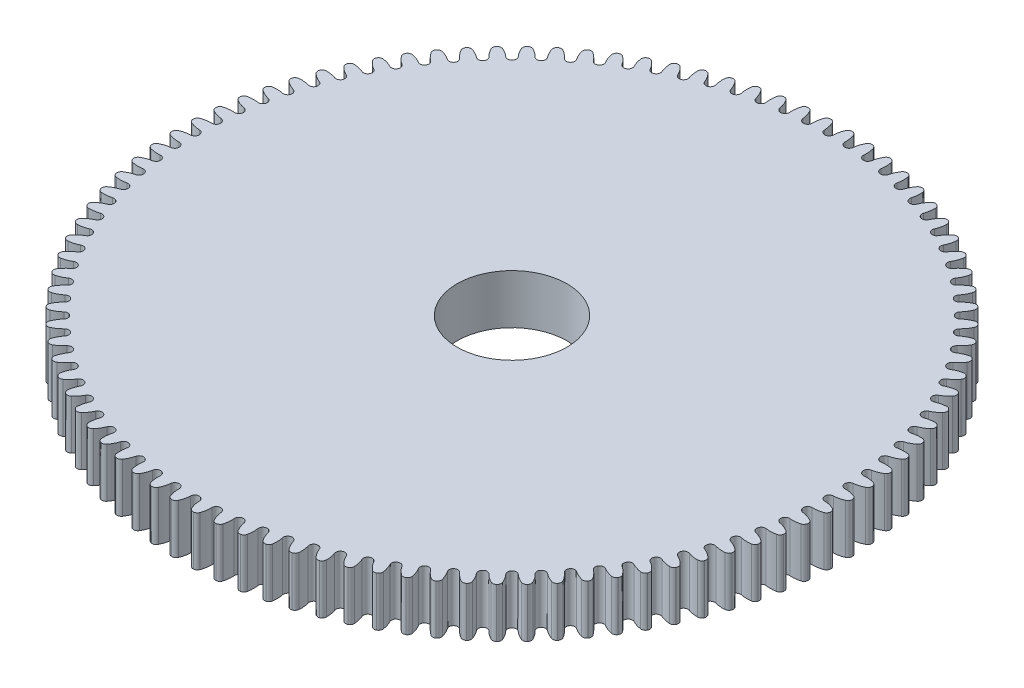
SolidWorks part; units mm, degrees
ref_plane "Front Plane" through (0, 0, 0) normal (0, 0, 1) x (1, 0, 0)
ref_plane "Top Plane" through (0, 0, 0) normal (0, 1, 0) x (1, 0, 0)
ref_plane "Right Plane" through (0, 0, 0) normal (1, 0, 0) x (0, 0, -1)
sketch "Sketch1" plane through (0, 0, 0) normal (0, 1, 0) x (1, 0, 0)
  circle A0 centre (0, 0) radius 60
  dimension "D1" = 120
extrude "Boss-Extrude1" add sketch "Sketch1" along normal blind 9
sketch "Sketch3" plane through (0, 0, 0) normal (0, -1, 0) x (1, 0, 0)
  line L0 (0, -57.718) -> (0, -60.2569) construction
  arc A0 (0.7992, -57.6813) -> (-0.7992, -57.6813) centre (0, -57.718) ccw
  arc A1 (0.7992, -57.6813) -> (1.2101, -59.4817) centre (5.9937, -57.4428) ccw
  circle A2 centre (1.946, -59.168) radius 0.8
  circle A3 centre (0, 0) radius 60 construction
  circle A4 centre (-1.946, -59.168) radius 0.8
  arc A5 (-0.7992, -57.6813) -> (-1.2101, -59.4817) centre (-5.9937, -57.4428) cw
  dimension "D1" = 1.6
  dimension "D2" = 10.4
  dimension "D3" = 1.45
  dimension "D4" = 1.6
  dimension "D5" = 3.892
extrude "Cut-Extrude1" cut sketch "Sketch3" against normal blind 9
pattern_circular "CirPattern1" count 96 over 360 about axis through (0, 0, 0) along (0, 1, 0) of "Cut-Extrude1"
sketch "Sketch4" plane through (0, 0, 0) normal (0, -1, 0) x (1, 0, 0)
  circle A0 centre (0, 0) radius 10
  dimension "D1" = 20
extrude "Cut-Extrude3" cut sketch "Sketch4" against normal blind 9
